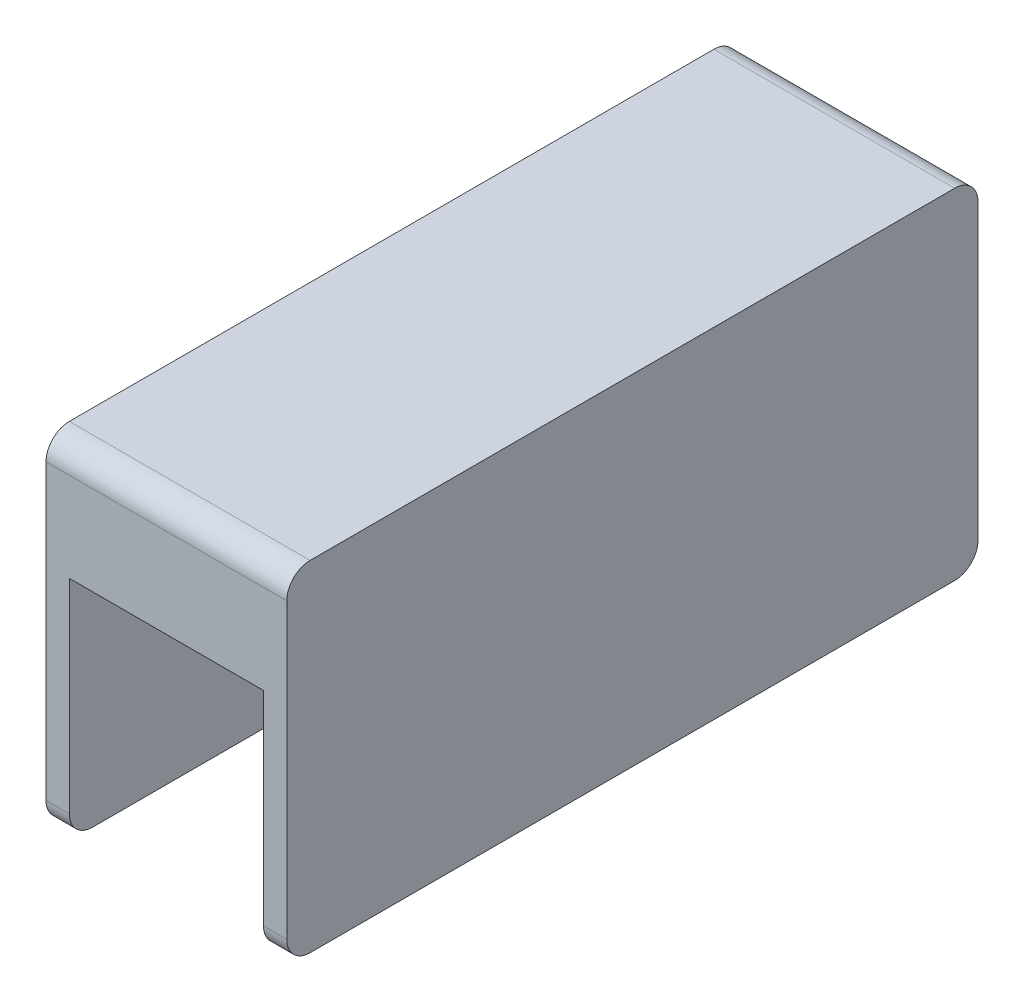
SolidWorks part; units mm, degrees
ref_plane "Plano frontal" through (0, 0, 0) normal (0, 0, 1) x (1, 0, 0)
ref_plane "Plano superior" through (0, 0, 0) normal (0, 1, 0) x (1, 0, 0)
ref_plane "Plano direito" through (0, 0, 0) normal (1, 0, 0) x (0, 0, -1)
sketch "Esboço2" plane through (0, 0, 0) normal (1, 0, 0) x (0, 0, -1)
  line L1 (2.9016, -0.0625) -> (-35.0984, -0.0625) construction
  line L2 (2.9016, -0.0625) -> (-35.0984, -0.0625)
  line L6 (7.6893, -0.0625) -> (2.9016, -0.0625)
  line L8 (-39.8861, -0.0625) -> (-35.0984, -0.0625)
  line L9 (-60.5984, 9.4769) -> (-60.5984, 20.9769)
  line L10 (28.4016, 9.4769) -> (28.4016, 20.9769)
  line L11 (-57.5984, 23.9769) -> (25.4016, 23.9769)
  arc A0 (28.4016, 20.9769) -> (25.4016, 23.9769) centre (25.4016, 20.9769) ccw
  arc A1 (-60.5984, 20.9769) -> (-57.5984, 23.9769) centre (-57.5984, 20.9769) cw
  arc A2 (28.4016, 9.4769) -> (24.5016, 12.3387) centre (25.4016, 9.4769) ccw
  arc A3 (-48.8914, 5.5897) -> (-56.6984, 12.3387) centre (-60.5984, -0.0625) ccw
  arc A4 (-48.8914, 5.5897) -> (-39.8861, -0.0625) centre (-39.8861, 9.9375) ccw
  arc A5 (-60.5984, 9.4769) -> (-56.6984, 12.3387) centre (-57.5984, 9.4769) cw
  arc A6 (16.6946, 5.5897) -> (7.6893, -0.0625) centre (7.6893, 9.9375) cw
  arc A7 (16.6946, 5.5897) -> (24.5016, 12.3387) centre (28.4016, -0.0625) cw
  point P22 (28.4016, 12.9375)
  point P23 (-60.5984, 12.9375)
  dimension "D1" = 3
extrude "Ressalto-extrusão2" add sketch "Esboço2" along normal blind 25
sketch "Esboço3" plane through (0, 0, 0) normal (-1, 0, 0) x (0, 0, 1)
  line L0 (60.5984, 15.2269) -> (60.5984, 20.9769)
  line L1 (60.5984, 20.9769) -> (60.5984, 9.4769) construction
  line L2 (-28.4016, 15.2269) -> (-28.4016, 20.9769)
  line L3 (-28.4016, 9.4769) -> (-28.4016, 20.9769) construction
  line L4 (16.0984, 23.9769) -> (57.5984, 23.9769)
  line L5 (-25.4016, 23.9769) -> (57.5984, 23.9769) construction
  line L6 (16.0984, 23.9769) -> (-25.4016, 23.9769)
  line L7 (60.5984, 15.2269) -> (60.5984, -16.7731)
  line L8 (-28.4016, 15.2269) -> (-28.4016, -16.7731)
  line L9 (57.5984, -19.7731) -> (-25.4016, -19.7731)
  arc A0 (57.5984, 23.9769) -> (60.5984, 20.9769) centre (57.5984, 20.9769) cw
  arc A1 (-28.4016, 20.9769) -> (-25.4016, 23.9769) centre (-25.4016, 20.9769) cw
  arc A2 (-28.4016, -16.7731) -> (-25.4016, -19.7731) centre (-25.4016, -16.7731) ccw
  arc A3 (60.5984, -16.7731) -> (57.5984, -19.7731) centre (57.5984, -16.7731) cw
  dimension "D1" = 3
  dimension "D2" = 3
extrude "Ressalto-extrusão3" add sketch "Esboço3" along normal blind 3
sketch "Esboço4" plane through (25, 0, 0) normal (1, 0, 0) x (0, 0, -1)
  line L0 (-16.0984, 23.9769) -> (25.4016, 23.9769)
  line L1 (25.4016, 23.9769) -> (-57.5984, 23.9769) construction
  line L2 (-16.0984, 23.9769) -> (-57.5984, 23.9769)
  line L3 (28.4016, 15.2269) -> (28.4016, 20.9769)
  line L4 (28.4016, 9.4769) -> (28.4016, 20.9769) construction
  line L5 (-60.5984, 20.9769) -> (-60.5984, 15.2269)
  line L7 (28.4016, 15.2269) -> (28.4016, -16.7731)
  line L8 (28.4016, 9.4769) -> (28.4016, -16.7731) construction
  line L9 (-60.5984, 20.9769) -> (-60.5984, 9.4769) construction
  line L10 (-60.5984, 15.2269) -> (-60.5984, -16.7731)
  line L11 (25.4016, -19.7731) -> (-57.5984, -19.7731)
  arc A0 (25.4016, 23.9769) -> (28.4016, 20.9769) centre (25.4016, 20.9769) cw
  arc A1 (-60.5984, 20.9769) -> (-57.5984, 23.9769) centre (-57.5984, 20.9769) cw
  arc A2 (-60.5984, -16.7731) -> (-57.5984, -19.7731) centre (-57.5984, -16.7731) ccw
  arc A3 (28.4016, -16.7731) -> (25.4016, -19.7731) centre (25.4016, -16.7731) cw
  point P23 (28.4016, -19.7731)
  dimension "D1" = 3
extrude "Ressalto-extrusão4" add sketch "Esboço4" along normal blind 3
